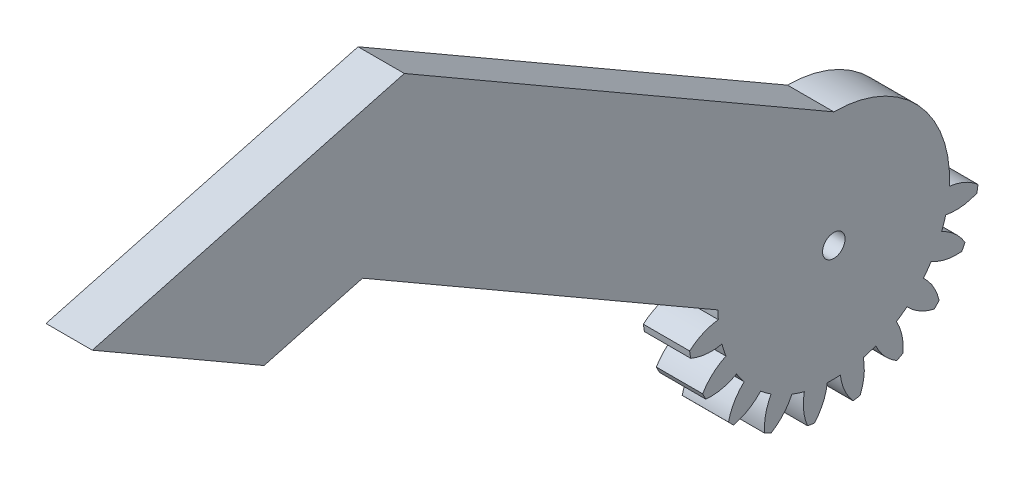
SolidWorks part; units mm, degrees
ref_plane "Plane1" through (0, 0, 0) normal (0, 0, 1) x (1, 0, 0)
ref_plane "Plane2" through (0, 0, 0) normal (0, 1, 0) x (1, 0, 0)
ref_plane "Plane3" through (0, 0, 0) normal (1, 0, 0) x (0, 0, -1)
other "Configuration Table"
sketch "HoldingSke" plane through (0, 0, 0) normal (0, 1, 0) x (1, 0, 0)
  line L0 (0, 0) -> (0.4698, -0.171)
  line L1 (-15, 0) -> (100, 0) construction
  line L2 (0, 0) -> (-2.1039, 2.3779)
  line L3 (0, 0) -> (-11.863, 4.5341)
  line L4 (0, 0) -> (8.1152, 2.9537)
  line L5 (0, 0) -> (-46.8476, -17.4728)
  line L6 (0, 0) -> (-12.4344, -8.3896)
  line L7 (-2.1039, 2.3779) -> (8.6586, 51.2059)
  line L8 (-76.2, 54.61) -> (-76.1, 54.61)
  line L9 (-71.009, 38.7566) -> (-53.1078, 45.2721)
  line L10 (-76.2, 71.12) -> (104.1128, 71.12)
  line L11 (0, 0) -> (-15, 0)
  line L12 (-76.2, 101.6) -> (-76.133, 101.6)
  line L13 (24.9733, 27.94) -> (52.9518, 28.4284)
  line L14 (24.9733, 27.94) -> (24.9743, 27.94)
  line L15 (24.9733, 27.94) -> (100.4006, 29.5858)
  line L16 (-63.627, -2) -> (-12.827, -2)
  circle A0 centre (0, 0) radius 0.5
  circle A1 centre (0, 0) radius 17.499
  circle A2 centre (0, 0) radius 37.5
  circle A3 centre (0, 0) radius 0.5
  dimension "MHD" = 34.998
  dimension "Hub_dia" = 75
  dimension "Bore" = 1
  dimension "MBD" = 1
  dimension "Num_teeth" = 20
  dimension "Pitch" = 0.5
  dimension "Overall_len" = 50
  dimension "Show_teeth" = 20
  dimension "Thickness" = 15
  dimension "OAL" = 50.0001
  dimension "T_dim" = 0.1
  dimension "Ap" = 20
  dimension "H" = 19.05
  dimension "Pitch_radius" = 180.3128
  dimension "Width" = 15
  dimension "Backlash" = 0.067
  dimension "Addendum_fac" = 1
  dimension "Dedendum_fac" = 1.25
  dimension "Clearance_fac" = 0.25
  dimension "Dedendum_add" = 0.001
  dimension "Module" = 2
sketch "BasProSke" plane through (0, 0, 0) normal (0, 1, 0) x (1, 0, 0)
  line L0 (-10, 0) -> (60, 0) construction
  line L1 (0, 0) -> (0, 22)
  line L2 (0, 0) -> (15, 0)
  line L3 (15, 0) -> (15, 22)
  line L4 (15, 22) -> (0, 22)
  dimension "Thickness" = 15
  dimension "Diameter" = 44
revolve "Base-Revolve" add sketch "BasProSke" angle 360 about L0
sketch "TooCutSke" plane through (0, 0, 0) normal (1, 0, 0) x (0, 0, -1)
  line L1 (0, 0) -> (0, 107) construction
  line L2 (0, 0) -> (-1.6864, 19.9288) construction
  line L3 (0, 0) -> (-6.2409, 39.4033) construction
  line L4 (-1.6864, 19.9288) -> (-3.1204, 19.7016) construction
  arc A0 (0.9862, 17.4712) -> (-0.9862, 17.4712) centre (0, 0) ccw
  arc A1 (2.9329, 21.8293) -> (-2.9329, 21.8293) centre (0, 0) ccw
  circle A2 centre (0, 0) radius 20 construction
  circle A3 centre (0, 0) radius 18.7939 construction
  arc A4 (-0.9862, 17.4712) -> (-2.9329, 21.8293) centre (-8.9313, 16.536) ccw
  arc A5 (2.9329, 21.8293) -> (0.9862, 17.4712) centre (8.9313, 16.536) ccw
  dimension "Root_dia" = 34.998
  dimension "Overcut_dia" = 44.0508
  dimension "Pitch_dia" = 40
  dimension "Base_dia" = 37.5877
  dimension "Flank_rad" = 8
  dimension "Half_ang" = 9
  dimension "Half_CT" = 1.4519
extrude "ToothCut" cut sketch "TooCutSke" along normal through all
fillet "Breaks" [suppressed] radius 0.04
fillet "RootFillets" [suppressed] radius 0.501
pattern_circular "TeethCuts" count 20 every 18 about axis through (-10, 0, 0) along (1, 0, 0) of "ToothCut", "RootFillets", "Breaks"
sketch "HubNeaOneSke" plane through (0, 0, 0) normal (-1, 0, 0) x (0, 0, 1)
  circle A0 centre (0, 0) radius 17.499
  dimension "Diameter" = 34.998
extrude "HubNearOne" [suppressed] add sketch "HubNeaOneSke" along normal blind 35.0001
sketch "HubNeaBotSke" plane through (0, 0, 0) normal (-1, 0, 0) x (0, 0, 1)
  circle A0 centre (0, 0) radius 17.499
  dimension "Diameter" = 34.998
extrude "HubNearBoth" [suppressed] add sketch "HubNeaBotSke" along normal blind 17.5
ref_plane "FarPln" through (15, 0, 0) normal (1, 0, 0) x (0, 0, -1)
sketch "HubFarSke" plane through (15, 0, 0) normal (1, 0, 0) x (0, 0, -1)
  circle A0 centre (0, 0) radius 17.499
  dimension "Diameter" = 34.998
extrude "HubFar" [suppressed] add sketch "HubFarSke" along normal blind 17.5
sketch "BorSke" plane through (0, 0, 0) normal (1, 0, 0) x (0, 0, -1)
  circle A0 centre (0, 0) radius 0.5
  dimension "Diameter" = 1
extrude "Bore" cut sketch "BorSke" along normal mid plane 100.0001
sketch "KeySke" plane through (0, 0, 0) normal (1, 0, 0) x (0, 0, -1)
  line L0 (-0.05, 0) -> (-0.05, 0.6)
  line L1 (-0.05, 0.6) -> (0.05, 0.6)
  line L2 (0.05, 0.6) -> (0.05, 0)
  line L3 (0, 0) -> (0, 34) construction
  line L4 (-0.05, 0) -> (0.05, 0)
  dimension "Offset" = 0.6
  dimension "Width" = 0.1
extrude "Keyway" [suppressed] cut sketch "KeySke" along normal mid plane 100.0001
pattern_circular "Keyway2" [suppressed] count 2 every 90 about axis through (-10, 0, 0) along (1, 0, 0)
sketch "Sketch1" plane through (0, 0, 0) normal (-1, 0, 0) x (0, 0, 1)
  circle A0 centre (0, 0) radius 11.1
extrude "Cut-Extrude1" cut sketch "Sketch1" against normal blind 16
sketch "Sketch2" plane through (0, 0, 0) normal (-1, 0, 0) x (0, 0, 1)
  arc A80 (17.4712, 0.9862) -> (21.8063, 2.9127) centre (16.536, 8.9313) ccw
  arc A81 (21.8063, 2.9127) -> (21.6391, 3.9684) centre (0, 0) ccw
  arc A82 (21.6391, 3.9684) -> (16.9208, 4.461) centre (18.4866, -3.3843) ccw
  arc A83 (16.9208, 4.461) -> (16.3113, 6.3368) centre (0, 0) ccw
  arc A84 (16.3113, 6.3368) -> (19.839, 9.5087) centre (12.9668, 13.6041) ccw
  arc A85 (19.839, 9.5087) -> (19.3537, 10.461) centre (0, 0) ccw
  arc A86 (19.3537, 10.461) -> (14.7141, 9.4715) centre (18.6276, 2.494) ccw
  arc A87 (14.7141, 9.4715) -> (13.5548, 11.0671) centre (0, 0) ccw
  arc A88 (13.5548, 11.0671) -> (15.9297, 15.1739) centre (8.1282, 16.9452) ccw
  arc A89 (15.9297, 15.1739) -> (15.1739, 15.9297) centre (0, 0) ccw
  arc A90 (15.1739, 15.9297) -> (11.0671, 13.5548) centre (16.9452, 8.1282) ccw
  arc A91 (11.0671, 13.5548) -> (9.4715, 14.7141) centre (0, 0) ccw
  arc A92 (9.4715, 14.7141) -> (10.461, 19.3537) centre (2.494, 18.6276) ccw
  arc A93 (10.461, 19.3537) -> (9.5087, 19.839) centre (0, 0) ccw
  arc A94 (9.5087, 19.839) -> (6.3368, 16.3113) centre (13.6041, 12.9668) ccw
  arc A95 (6.3368, 16.3113) -> (4.461, 16.9208) centre (0, 0) ccw
  arc A96 (4.461, 16.9208) -> (3.9684, 21.6391) centre (-3.3843, 18.4866) ccw
  arc A97 (3.9684, 21.6391) -> (2.9127, 21.8063) centre (0, 0) ccw
  arc A98 (2.9127, 21.8063) -> (0.9862, 17.4712) centre (8.9313, 16.536) ccw
  arc A99 (0.9862, 17.4712) -> (-0.9862, 17.4712) centre (0, 0) ccw
  arc A100 (-0.9862, 17.4712) -> (-2.9127, 21.8063) centre (-8.9313, 16.536) ccw
  arc A101 (-2.9127, 21.8063) -> (-3.9684, 21.6391) centre (0, 0) ccw
  arc A102 (-3.9684, 21.6391) -> (-4.461, 16.9208) centre (3.3843, 18.4866) ccw
  arc A103 (-4.461, 16.9208) -> (-6.3368, 16.3113) centre (0, 0) ccw
  arc A104 (-6.3368, 16.3113) -> (-9.5087, 19.839) centre (-13.6041, 12.9668) ccw
  arc A105 (-9.5087, 19.839) -> (-10.461, 19.3537) centre (0, 0) ccw
  arc A106 (-10.461, 19.3537) -> (-9.4715, 14.7141) centre (-2.494, 18.6276) ccw
  arc A107 (-9.4715, 14.7141) -> (-11.0671, 13.5548) centre (0, 0) ccw
  arc A108 (-11.0671, 13.5548) -> (-15.1739, 15.9297) centre (-16.9452, 8.1282) ccw
  arc A109 (-15.1739, 15.9297) -> (-15.9297, 15.1739) centre (0, 0) ccw
  arc A110 (-15.9297, 15.1739) -> (-13.5548, 11.0671) centre (-8.1282, 16.9452) ccw
  arc A111 (-13.5548, 11.0671) -> (-14.7141, 9.4715) centre (0, 0) ccw
  arc A112 (-14.7141, 9.4715) -> (-19.3537, 10.461) centre (-18.6276, 2.494) ccw
  arc A113 (-19.3537, 10.461) -> (-19.839, 9.5087) centre (0, 0) ccw
  arc A114 (-19.839, 9.5087) -> (-16.3113, 6.3368) centre (-12.9668, 13.6041) ccw
  arc A115 (-16.3113, 6.3368) -> (-16.9208, 4.461) centre (0, 0) ccw
  arc A116 (-16.9208, 4.461) -> (-21.6391, 3.9684) centre (-18.4866, -3.3843) ccw
  arc A117 (-21.6391, 3.9684) -> (-21.8063, 2.9127) centre (0, 0) ccw
  arc A118 (-21.8063, 2.9127) -> (-17.4712, 0.9862) centre (-16.536, 8.9313) ccw
  arc A119 (-17.4712, 0.9862) -> (-17.4712, -0.9862) centre (0, 0) ccw
  arc A120 (-17.4712, -0.9862) -> (-21.8063, -2.9127) centre (-16.536, -8.9313) ccw
  arc A121 (-21.8063, -2.9127) -> (-21.6391, -3.9684) centre (0, 0) ccw
  arc A122 (-21.6391, -3.9684) -> (-16.9208, -4.461) centre (-18.4866, 3.3843) ccw
  arc A123 (-16.9208, -4.461) -> (-16.3113, -6.3368) centre (0, 0) ccw
  arc A124 (-16.3113, -6.3368) -> (-19.839, -9.5087) centre (-12.9668, -13.6041) ccw
  arc A125 (-19.839, -9.5087) -> (-19.3537, -10.461) centre (0, 0) ccw
  arc A126 (-19.3537, -10.461) -> (-14.7141, -9.4715) centre (-18.6276, -2.494) ccw
  arc A127 (-14.7141, -9.4715) -> (-13.5548, -11.0671) centre (0, 0) ccw
  arc A128 (-13.5548, -11.0671) -> (-15.9297, -15.1739) centre (-8.1282, -16.9452) ccw
  arc A129 (-15.9297, -15.1739) -> (-15.1739, -15.9297) centre (0, 0) ccw
  arc A130 (-15.1739, -15.9297) -> (-11.0671, -13.5548) centre (-16.9452, -8.1282) ccw
  arc A131 (-11.0671, -13.5548) -> (-9.4715, -14.7141) centre (0, 0) ccw
  arc A132 (-9.4715, -14.7141) -> (-10.461, -19.3537) centre (-2.494, -18.6276) ccw
  arc A133 (-10.461, -19.3537) -> (-9.5087, -19.839) centre (0, 0) ccw
  arc A134 (-9.5087, -19.839) -> (-6.3368, -16.3113) centre (-13.6041, -12.9668) ccw
  arc A135 (-6.3368, -16.3113) -> (-4.461, -16.9208) centre (0, 0) ccw
  arc A136 (-4.461, -16.9208) -> (-3.9684, -21.6391) centre (3.3843, -18.4866) ccw
  arc A137 (-3.9684, -21.6391) -> (-2.9127, -21.8063) centre (0, 0) ccw
  arc A138 (-2.9127, -21.8063) -> (-0.9862, -17.4712) centre (-8.9313, -16.536) ccw
  arc A139 (-0.9862, -17.4712) -> (0.9862, -17.4712) centre (0, 0) ccw
  arc A140 (0.9862, -17.4712) -> (2.9127, -21.8063) centre (8.9313, -16.536) ccw
  arc A141 (2.9127, -21.8063) -> (3.9684, -21.6391) centre (0, 0) ccw
  arc A142 (3.9684, -21.6391) -> (4.461, -16.9208) centre (-3.3843, -18.4866) ccw
  arc A143 (4.461, -16.9208) -> (6.3368, -16.3113) centre (0, 0) ccw
  arc A144 (6.3368, -16.3113) -> (9.5087, -19.839) centre (13.6041, -12.9668) ccw
  arc A145 (9.5087, -19.839) -> (10.461, -19.3537) centre (0, 0) ccw
  arc A146 (10.461, -19.3537) -> (9.4715, -14.7141) centre (2.494, -18.6276) ccw
  arc A147 (9.4715, -14.7141) -> (11.0671, -13.5548) centre (0, 0) ccw
  arc A148 (11.0671, -13.5548) -> (15.1739, -15.9297) centre (16.9452, -8.1282) ccw
  arc A149 (15.1739, -15.9297) -> (15.9297, -15.1739) centre (0, 0) ccw
  arc A150 (15.9297, -15.1739) -> (13.5548, -11.0671) centre (8.1282, -16.9452) ccw
  arc A151 (13.5548, -11.0671) -> (14.7141, -9.4715) centre (0, 0) ccw
  arc A152 (14.7141, -9.4715) -> (19.3537, -10.461) centre (18.6276, -2.494) ccw
  arc A153 (19.3537, -10.461) -> (19.839, -9.5087) centre (0, 0) ccw
  arc A154 (19.839, -9.5087) -> (16.3113, -6.3368) centre (12.9668, -13.6041) ccw
  arc A155 (16.3113, -6.3368) -> (16.9208, -4.461) centre (0, 0) ccw
  arc A156 (16.9208, -4.461) -> (21.6391, -3.9684) centre (18.4866, 3.3843) ccw
  arc A157 (21.6391, -3.9684) -> (21.8063, -2.9127) centre (0, 0) ccw
  arc A158 (21.8063, -2.9127) -> (17.4712, -0.9862) centre (16.536, -8.9313) ccw
  arc A159 (17.4712, -0.9862) -> (17.4712, 0.9862) centre (0, 0) ccw
  arc A160 (17.4712, 0.9862) -> (21.8063, 2.9127) centre (16.536, 8.9313) ccw
  arc A161 (21.8063, 2.9127) -> (21.6391, 3.9684) centre (0, 0) ccw
  arc A162 (21.6391, 3.9684) -> (16.9208, 4.461) centre (18.4866, -3.3843) ccw
  arc A163 (16.9208, 4.461) -> (16.3113, 6.3368) centre (0, 0) ccw
  arc A164 (16.3113, 6.3368) -> (19.839, 9.5087) centre (12.9668, 13.6041) ccw
  arc A165 (19.839, 9.5087) -> (19.3537, 10.461) centre (0, 0) ccw
  arc A166 (19.3537, 10.461) -> (14.7141, 9.4715) centre (18.6276, 2.494) ccw
  arc A167 (14.7141, 9.4715) -> (13.5548, 11.0671) centre (0, 0) ccw
  arc A168 (13.5548, 11.0671) -> (15.9297, 15.1739) centre (8.1282, 16.9452) ccw
  arc A169 (15.9297, 15.1739) -> (15.1739, 15.9297) centre (0, 0) ccw
  arc A170 (15.1739, 15.9297) -> (11.0671, 13.5548) centre (16.9452, 8.1282) ccw
  arc A171 (11.0671, 13.5548) -> (9.4715, 14.7141) centre (0, 0) ccw
  arc A172 (9.4715, 14.7141) -> (10.461, 19.3537) centre (2.494, 18.6276) ccw
  arc A173 (10.461, 19.3537) -> (9.5087, 19.839) centre (0, 0) ccw
  arc A174 (9.5087, 19.839) -> (6.3368, 16.3113) centre (13.6041, 12.9668) ccw
  arc A175 (6.3368, 16.3113) -> (4.461, 16.9208) centre (0, 0) ccw
  arc A176 (4.461, 16.9208) -> (3.9684, 21.6391) centre (-3.3843, 18.4866) ccw
  arc A177 (3.9684, 21.6391) -> (2.9127, 21.8063) centre (0, 0) ccw
  arc A178 (2.9127, 21.8063) -> (0.9862, 17.4712) centre (8.9313, 16.536) ccw
  arc A179 (0.9862, 17.4712) -> (-0.9862, 17.4712) centre (0, 0) ccw
  arc A180 (-0.9862, 17.4712) -> (-2.9127, 21.8063) centre (-8.9313, 16.536) ccw
  arc A181 (-2.9127, 21.8063) -> (-3.9684, 21.6391) centre (0, 0) ccw
  arc A182 (-3.9684, 21.6391) -> (-4.461, 16.9208) centre (3.3843, 18.4866) ccw
  arc A183 (-4.461, 16.9208) -> (-6.3368, 16.3113) centre (0, 0) ccw
  arc A184 (-6.3368, 16.3113) -> (-9.5087, 19.839) centre (-13.6041, 12.9668) ccw
  arc A185 (-9.5087, 19.839) -> (-10.461, 19.3537) centre (0, 0) ccw
  arc A186 (-10.461, 19.3537) -> (-9.4715, 14.7141) centre (-2.494, 18.6276) ccw
  arc A187 (-9.4715, 14.7141) -> (-11.0671, 13.5548) centre (0, 0) ccw
  arc A188 (-11.0671, 13.5548) -> (-15.1739, 15.9297) centre (-16.9452, 8.1282) ccw
  arc A189 (-15.1739, 15.9297) -> (-15.9297, 15.1739) centre (0, 0) ccw
  arc A190 (-15.9297, 15.1739) -> (-13.5548, 11.0671) centre (-8.1282, 16.9452) ccw
  arc A191 (-13.5548, 11.0671) -> (-14.7141, 9.4715) centre (0, 0) ccw
  arc A192 (-14.7141, 9.4715) -> (-19.3537, 10.461) centre (-18.6276, 2.494) ccw
  arc A193 (-19.3537, 10.461) -> (-19.839, 9.5087) centre (0, 0) ccw
  arc A194 (-19.839, 9.5087) -> (-16.3113, 6.3368) centre (-12.9668, 13.6041) ccw
  arc A195 (-16.3113, 6.3368) -> (-16.9208, 4.461) centre (0, 0) ccw
  arc A196 (-16.9208, 4.461) -> (-21.6391, 3.9684) centre (-18.4866, -3.3843) ccw
  arc A197 (-21.6391, 3.9684) -> (-21.8063, 2.9127) centre (0, 0) ccw
  arc A198 (-21.8063, 2.9127) -> (-17.4712, 0.9862) centre (-16.536, 8.9313) ccw
  arc A199 (-17.4712, 0.9862) -> (-17.4712, -0.9862) centre (0, 0) ccw
  arc A200 (-17.4712, -0.9862) -> (-21.8063, -2.9127) centre (-16.536, -8.9313) ccw
  arc A201 (-21.8063, -2.9127) -> (-21.6391, -3.9684) centre (0, 0) ccw
  arc A202 (-21.6391, -3.9684) -> (-16.9208, -4.461) centre (-18.4866, 3.3843) ccw
  arc A203 (-16.9208, -4.461) -> (-16.3113, -6.3368) centre (0, 0) ccw
  arc A204 (-16.3113, -6.3368) -> (-19.839, -9.5087) centre (-12.9668, -13.6041) ccw
  arc A205 (-19.839, -9.5087) -> (-19.3537, -10.461) centre (0, 0) ccw
  arc A206 (-19.3537, -10.461) -> (-14.7141, -9.4715) centre (-18.6276, -2.494) ccw
  arc A207 (-14.7141, -9.4715) -> (-13.5548, -11.0671) centre (0, 0) ccw
  arc A208 (-13.5548, -11.0671) -> (-15.9297, -15.1739) centre (-8.1282, -16.9452) ccw
  arc A209 (-15.9297, -15.1739) -> (-15.1739, -15.9297) centre (0, 0) ccw
  arc A210 (-15.1739, -15.9297) -> (-11.0671, -13.5548) centre (-16.9452, -8.1282) ccw
  arc A211 (-11.0671, -13.5548) -> (-9.4715, -14.7141) centre (0, 0) ccw
  arc A212 (-9.4715, -14.7141) -> (-10.461, -19.3537) centre (-2.494, -18.6276) ccw
  arc A213 (-10.461, -19.3537) -> (-9.5087, -19.839) centre (0, 0) ccw
  arc A214 (-9.5087, -19.839) -> (-6.3368, -16.3113) centre (-13.6041, -12.9668) ccw
  arc A215 (-6.3368, -16.3113) -> (-4.461, -16.9208) centre (0, 0) ccw
  arc A216 (-4.461, -16.9208) -> (-3.9684, -21.6391) centre (3.3843, -18.4866) ccw
  arc A217 (-3.9684, -21.6391) -> (-2.9127, -21.8063) centre (0, 0) ccw
  arc A218 (-2.9127, -21.8063) -> (-0.9862, -17.4712) centre (-8.9313, -16.536) ccw
  arc A219 (-0.9862, -17.4712) -> (0.9862, -17.4712) centre (0, 0) ccw
  arc A220 (0.9862, -17.4712) -> (2.9127, -21.8063) centre (8.9313, -16.536) ccw
  arc A221 (2.9127, -21.8063) -> (3.9684, -21.6391) centre (0, 0) ccw
  arc A222 (3.9684, -21.6391) -> (4.461, -16.9208) centre (-3.3843, -18.4866) ccw
  arc A223 (4.461, -16.9208) -> (6.3368, -16.3113) centre (0, 0) ccw
  arc A224 (6.3368, -16.3113) -> (9.5087, -19.839) centre (13.6041, -12.9668) ccw
  arc A225 (9.5087, -19.839) -> (10.461, -19.3537) centre (0, 0) ccw
  arc A226 (10.461, -19.3537) -> (9.4715, -14.7141) centre (2.494, -18.6276) ccw
  arc A227 (9.4715, -14.7141) -> (11.0671, -13.5548) centre (0, 0) ccw
  arc A228 (11.0671, -13.5548) -> (15.1739, -15.9297) centre (16.9452, -8.1282) ccw
  arc A229 (15.1739, -15.9297) -> (15.9297, -15.1739) centre (0, 0) ccw
  arc A230 (15.9297, -15.1739) -> (13.5548, -11.0671) centre (8.1282, -16.9452) ccw
  arc A231 (13.5548, -11.0671) -> (14.7141, -9.4715) centre (0, 0) ccw
  arc A232 (14.7141, -9.4715) -> (19.3537, -10.461) centre (18.6276, -2.494) ccw
  arc A233 (19.3537, -10.461) -> (19.839, -9.5087) centre (0, 0) ccw
  arc A234 (19.839, -9.5087) -> (16.3113, -6.3368) centre (12.9668, -13.6041) ccw
  arc A235 (16.3113, -6.3368) -> (16.9208, -4.461) centre (0, 0) ccw
  arc A236 (16.9208, -4.461) -> (21.6391, -3.9684) centre (18.4866, 3.3843) ccw
  arc A237 (21.6391, -3.9684) -> (21.8063, -2.9127) centre (0, 0) ccw
  arc A238 (21.8063, -2.9127) -> (17.4712, -0.9862) centre (16.536, -8.9313) ccw
  arc A239 (17.4712, -0.9862) -> (17.4712, 0.9862) centre (0, 0) ccw
  dimension "D1" = 0
extrude "Cut-Extrude2" cut sketch "Sketch2" against normal blind 8
sketch "Sketch3" plane through (8, 0, 0) normal (-1, 0, 0) x (0, 0, 1)
  circle A0 centre (0, 0) radius 11.1
extrude "Boss-Extrude2" add sketch "Sketch3" against normal blind 7
sketch "Sketch5" plane through (8, 0, 0) normal (-1, 0, 0) x (0, 0, 1)
  line L1 (-29.6013, 0) -> (27.3976, 0)
  line L2 (-29.6013, 0) -> (-29.6013, 22.7221)
  line L3 (-29.6013, 22.7221) -> (27.3976, 22.7221)
  line L4 (27.3976, 0) -> (27.3976, 22.7221)
extrude "Cut-Extrude3" cut sketch "Sketch5" against normal blind 7
sketch "Sketch6" plane through (8, 0, 0) normal (-1, 0, 0) x (0, 0, 1)
  line L0 (-17.499, 0) -> (17.499, 0) construction
  circle A0 centre (0, 0) radius 17.499
extrude "Boss-Extrude3" add sketch "Sketch6" against normal blind 7
sketch "Sketch7" plane through (8, 0, 0) normal (-1, 0, 0) x (0, 0, 1)
  circle A0 centre (0, 0) radius 1.7
extrude "Cut-Extrude4" cut sketch "Sketch7" against normal blind 7
sketch "Sketch8" plane through (8, 0, 0) normal (-1, 0, 0) x (0, 0, 1)
  line L0 (0, 17.499) -> (64.9519, 54.999)
  line L1 (0, 17.499) -> (100.4628, 17.499) construction
  line L2 (0, 0) -> (15.5563, -15.5563) construction
  line L3 (15.5563, -15.5563) -> (145.4602, 59.4437) construction
  line L4 (64.9519, 54.999) -> (112.1481, 42.3528)
  line L5 (71.269, 31.3448) -> (86.1674, 27.3528)
  line L6 (86.1674, 27.3528) -> (112.1481, 42.3528)
  line L7 (17.4964, 0.2992) -> (71.269, 31.3448)
  line L8 (0, 0) -> (14.1985, -14.1985) construction
  line L9 (14.1985, -14.1985) -> (123.8485, 49.1081) construction
  arc A0 (15.1739, -15.9297) -> (15.9297, -15.1739) centre (0, 0) ccw construction
  arc A1 (17.4712, -0.9862) -> (-17.4712, -0.9862) centre (0, 0) ccw construction
  circle A2 centre (0, 0) radius 17.499
  circle A4 centre (0, 0) radius 17.499
  dimension "D1" = 30
  dimension "D2" = 75
extrude "Boss-Extrude5" add sketch "Sketch8" against normal blind 7
equation "' \"Module@HoldingSke\" = 6.35"
equation "' \"Num_teeth@HoldingSke\" = 12"
equation "' \"Ap@HoldingSke\" =  20"
equation "' \"Ap@HoldingSke\" = 20"
equation "' \"Width@HoldingSke\" = 0.5 * 25.4"
equation "' \"Hub_dia@HoldingSke\"= 1 * 25.4"
equation "' \"Hub_dia@HoldingSke\" = 1 * 25.4"
equation "' \"Overall_len@HoldingSke\" = 1.0 * 25.4"
equation "' \"Bore@HoldingSke\" = 0.75 * 25.4"
equation "' \"T_dim@HoldingSke\" = 0.1 * 25.4"
equation "' \"Width@KeySke\" = 0.25 * 25.4"
equation "' \"Show_teeth@HoldingSke\" = 13"
equation "' \"Backlash@HoldingSke\" = 0.009 * 25.4"
equation "' \"Addendum_fac@HoldingSke\" = 1.0"
equation "' \"Dedendum_fac@HoldingSke\" = 1.25"
equation "' \"Dedendum_add@HoldingSke\" = 0.00005 * 25.4"
equation "' \"Clearance_fac@HoldingSke\" = 0.25"
equation "\"Pitch@HoldingSke\" = 1 / \"Module@HoldingSke\""
equation "\"Overcut_dia@TooCutSke\" = (\"Num_teeth@HoldingSke\" + 2 * \"Addendum_fac@HoldingSke\") / \"Pitch@HoldingSke\" + 0.002 * 25.4"
equation "\"Pitch_dia@TooCutSke\" = \"Num_teeth@HoldingSke\" / \"Pitch@HoldingSke\""
equation "\"Base_dia@TooCutSke\" = \"Num_teeth@HoldingSke\" / \"Pitch@HoldingSke\" * cos((\"Ap@HoldingSke\"  * 3.14159265 / 180))"
equation "\"Root_dia@TooCutSke\" = (\"Num_teeth@HoldingSke\" + 2) / \"Pitch@HoldingSke\" - 2 * (\"Addendum_fac@HoldingSke\" + \"Dedendum_fac@HoldingSke\") / \"Pitch@HoldingSke\" - \"Dedendum_add@HoldingSke\" * 2"
equation "\"Half_ang@TooCutSke\" = 180 / \"Num_teeth@HoldingSke\""
equation "\"Half_CT@TooCutSke\" = \"Num_teeth@HoldingSke\" / \"Pitch@HoldingSke\" * sin((3.14159265 / 2 / \"Num_teeth@HoldingSke\")) / 2 - 7 * \"Backlash@HoldingSke\" / 4"
equation "\"Flank_rad@TooCutSke\" = \"Num_teeth@HoldingSke\" / \"Pitch@HoldingSke\" / 5"
equation "\"Radius@RootFillets\" = \"Clearance_fac@HoldingSke\" / \"Pitch@HoldingSke\" + \"Dedendum_add@HoldingSke\""
equation "\"Break_rad@Breaks\" = 0.02 / \"Pitch@HoldingSke\""
equation "\"Thickness@HoldingSke\" = \"Width@HoldingSke\""
equation "\"OAL@HoldingSke\" = \"Thickness@HoldingSke\""
equation "\"MHD@HoldingSke\" = (\"Num_teeth@HoldingSke\" + 2) / \"Pitch@HoldingSke\" - 2 * (\"Addendum_fac@HoldingSke\" + \"Dedendum_fac@HoldingSke\")  / \"Pitch@HoldingSke\" - \"Dedendum_add@HoldingSke\" * 2"
equation "\"MBD@HoldingSke\" = (\"Num_teeth@HoldingSke\" + 2) / \"Pitch@HoldingSke\" - 2 * (\"Addendum_fac@HoldingSke\" + \"Dedendum_fac@HoldingSke\")  / \"Pitch@HoldingSke\" - \"Dedendum_add@HoldingSke\" * 2 - 0.002 * 25.4"
equation "\"MHD@HoldingSke\" = ((sgn( \"MHD@HoldingSke\" - \"Hub_dia@HoldingSke\" )-1)*( \"MHD@HoldingSke\" - \"Hub_dia@HoldingSke\" ))/-2+ \"Hub_dia@HoldingSke\""
equation "\"MBD@HoldingSke\" = ((sgn( \"MBD@HoldingSke\" - \"Bore@HoldingSke\" )-1)*( \"MBD@HoldingSke\" - \"Bore@HoldingSke\" ))/-2+ \"Bore@HoldingSke\""
equation "\"OAL@HoldingSke\" = ((sgn( \"OAL@HoldingSke\" - \"Overall_len@HoldingSke\" )+1)*( \"OAL@HoldingSke\" - \"Overall_len@HoldingSke\" ))/2 + \"Overall_len@HoldingSke\" + 0.000002 * 25.4"
equation "\"Num_teeth@TeethCuts\" = int( \"Show_teeth@HoldingSke\" ) + 1"
equation "\"Num_teeth@TeethCuts\" = ((sgn( \"Num_teeth@TeethCuts\" - \"Num_teeth@HoldingSke\" )-1)*( \"Num_teeth@TeethCuts\" - \"Num_teeth@HoldingSke\" ))/-2+ \"Num_teeth@HoldingSke\""
equation "\"Num_teeth@TeethCuts\" = ((sgn( \"Num_teeth@TeethCuts\" - 2.0)+1)*( \"Num_teeth@TeethCuts\" - 2.0))/2 +2.0"
equation "\"Angle@TeethCuts\" = 360.0 / \"Num_teeth@HoldingSke\""
equation "\"Diameter@BasProSke\" = (\"Num_teeth@HoldingSke\" + 2 * \"Addendum_fac@HoldingSke\") / \"Pitch@HoldingSke\""
equation "\"Thickness@BasProSke\"  = \"Thickness@HoldingSke\""
equation "' \"Fillet_rad@BasProSke\" =  \"Thickness@HoldingSke\" * 0.05"
equation "' \"Fillet_rad@BasProSke\" = \"Thickness@HoldingSke\" * 0.05"
equation "\"MHD@HoldingSke\" = ((sgn( \"MHD@HoldingSke\" - \"Root_dia@TooCutSke\" )-1)*( \"MHD@HoldingSke\" - \"Root_dia@TooCutSke\" ))/-2+ \"Root_dia@TooCutSke\""
equation "\"Diameter@HubNeaOneSke\" = \"MHD@HoldingSke\""
equation "\"Length@HubNearOne\" = \"OAL@HoldingSke\" - \"Thickness@BasProSke\""
equation "\"Diameter@HubNeaBotSke\" = \"MHD@HoldingSke\""
equation "\"Length@HubNearBoth\" = ( \"OAL@HoldingSke\" - \"Thickness@BasProSke\" ) / 2.0"
equation "\"Thickness@FarPln\" = \"Thickness@BasProSke\""
equation "\"Diameter@HubFarSke\" = \"MHD@HoldingSke\""
equation "\"Length@HubFar\" = ( \"OAL@HoldingSke\" - \"Thickness@BasProSke\" ) / 2.0"
equation "\"Diameter@BorSke\" = \"MBD@HoldingSke\""
equation "\"D1@Bore\" = \"OAL@HoldingSke\" * 2.0"
equation "\"D1@Keyway\" = \"OAL@HoldingSke\" * 2.0"
equation "\"Offset@KeySke\" = \"T_dim@HoldingSke\" + \"MBD@HoldingSke\" / 2.0"
